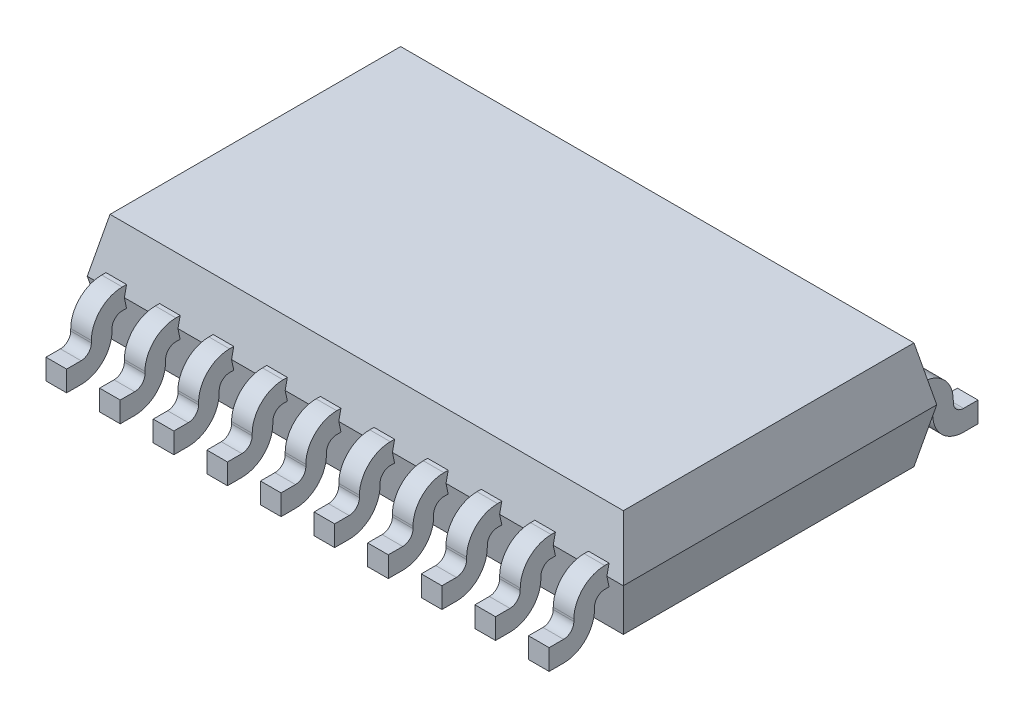
SolidWorks part; units mm, degrees
ref_plane "Front Plane" through (0, 0, 0) normal (0, 0, 1) x (1, 0, 0)
ref_plane "Top Plane" through (0, 0, 0) normal (0, 1, 0) x (1, 0, 0)
ref_plane "Right Plane" through (0, 0, 0) normal (1, 0, 0) x (0, 0, -1)
sketch "Sketch1" plane through (0, 0, 0) normal (0, 1, 0) x (1, 0, 0)
  line L1 (-6.5, 3.8) -> (6.5, 3.8)
  line L2 (-6.5, 3.8) -> (-6.5, -3.8)
  line L3 (-6.5, -3.8) -> (6.5, -3.8)
  line L4 (6.5, 3.8) -> (6.5, -3.8)
  line L5 (-6.5, 3.8) -> (6.5, -3.8) construction
  line L6 (-6.5, -3.8) -> (6.5, 3.8) construction
  point P0 (0, 0)
  dimension "D1" = 13
  dimension "D2" = 7.6
extrude "Boss-Extrude1" add sketch "Sketch1" along normal mid plane 2.6 draft 12
ref_plane "Plane1" through (0, 0, 3.8) normal (0, 0, 1) x (1, 0, 0)
sketch "Sketch2" plane through (0, 0, 3.8) normal (0, 0, 1) x (1, 0, 0)
  line L0 (-6.5, 0) -> (6.5, 0) construction
  line L1 (5.6, 0.25) -> (6.1, 0.25)
  line L2 (5.6, 0.25) -> (5.6, -0.25)
  line L3 (5.6, -0.25) -> (6.1, -0.25)
  line L4 (6.1, 0.25) -> (6.1, -0.25)
  line L5 (5.6, 0.25) -> (6.1, -0.25) construction
  line L6 (5.6, -0.25) -> (6.1, 0.25) construction
  point P0 (5.85, 0)
  dimension "D1" = 0.5
  dimension "D2" = 0.4
  dimension "D3" = 0.5
extrude "Boss-Extrude3" add sketch "Sketch2" along normal blind 0.8 and the other way blind 1 separate body
sketch "Sketch3" plane through (0, -0.25, 0) normal (0, -1, 0) x (-1, 0, 0)
  line L0 (-5.6, -2.8) -> (-5.6, -4.6) construction
  line L1 (-6.1, -4.6) -> (-5.6, -4.6)
  line L2 (-6.1, -4.6) -> (-6.1, -4.1)
  line L3 (-6.1, -4.1) -> (-5.6, -4.1)
  line L4 (-5.6, -4.6) -> (-5.6, -4.1)
  dimension "D1" = 0.5
extrude "Boss-Extrude4" add sketch "Sketch3" along normal up to surface (1.05 mm away) up to face at (0, -1.3, 0)
sketch "Sketch4" plane through (0, 0, 4.6) normal (0, 0, 1) x (1, 0, 0)
  line L0 (5.6, 0.25) -> (5.6, -1.3) construction
  line L1 (6.1, -1.3) -> (5.6, -1.3)
  line L2 (6.1, -1.3) -> (6.1, -0.8)
  line L3 (6.1, -0.8) -> (5.6, -0.8)
  line L4 (5.6, -1.3) -> (5.6, -0.8)
  dimension "D1" = 0.5
extrude "Boss-Extrude5" add sketch "Sketch4" along normal blind 0.6
fillet "Fillet1" radius 0.25 2 edges at (5.85, -0.8, 4.6) (5.85, -0.25, 4.1)
fillet "Fillet2" radius 0.75 2 edges at (5.85, -1.3, 4.1) (5.85, 0.25, 4.6)
pattern_linear "LPattern2" count 10 spacing 1.3 along (-1, 0, 0) of bodies 104
mirror "Mirror2" about plane through (0, 0, 0) normal (0, 0, 1) of bodies 111 104 105 106 107 108 109 110 112 113
